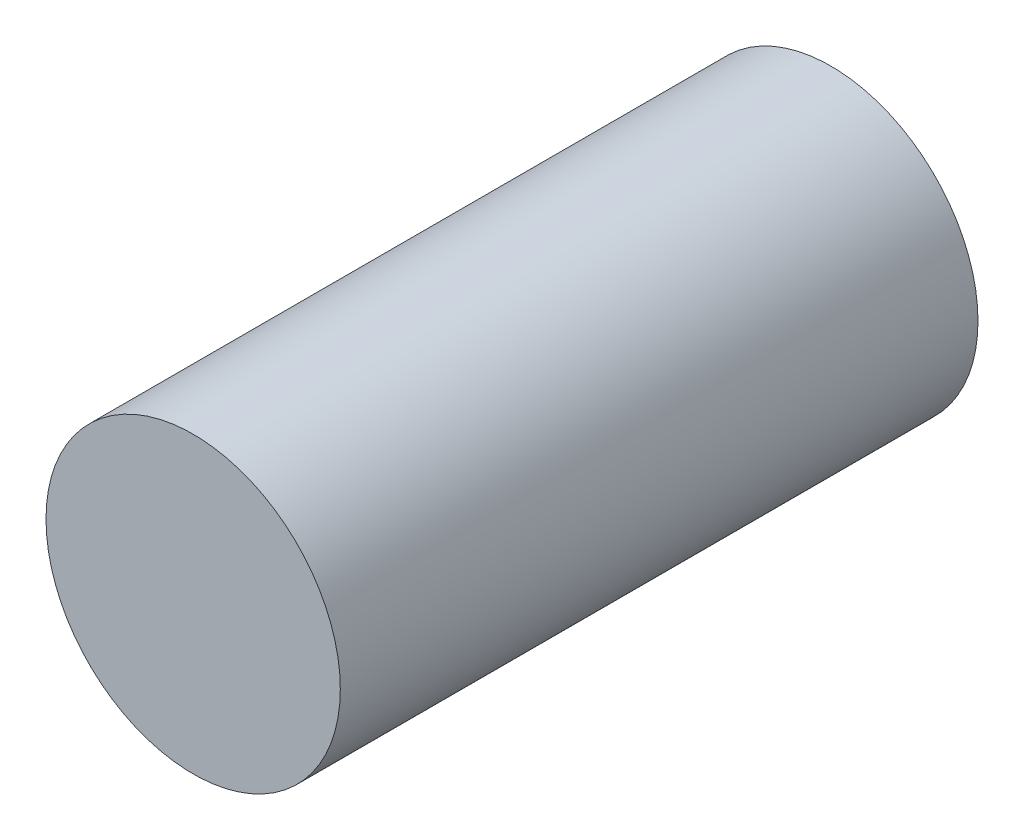
SolidWorks part; units mm, degrees
ref_plane "Front Plane" through (0, 0, 0) normal (0, 0, 1) x (1, 0, 0)
ref_plane "Top Plane" through (0, 0, 0) normal (0, 1, 0) x (1, 0, 0)
ref_plane "Right Plane" through (0, 0, 0) normal (1, 0, 0) x (0, 0, -1)
sketch "Sketch1" plane through (0, 0, 0) normal (0, 0, 1) x (1, 0, 0)
  circle A0 centre (0, 0) radius 30
  dimension "D1" = 60
extrude "Boss-Extrude1" add sketch "Sketch1" along normal blind 130
